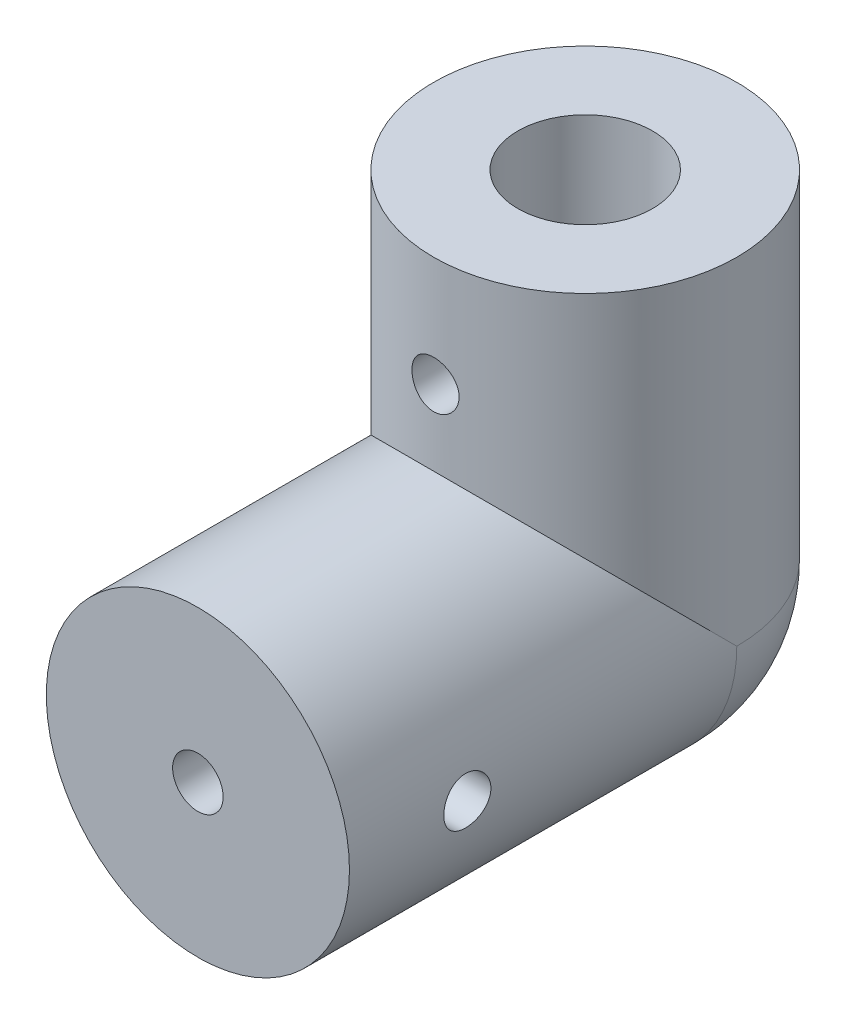
SolidWorks part; units mm, degrees
ref_plane "Alzado" through (0, 0, 0) normal (0, 0, 1) x (1, 0, 0)
ref_plane "Planta" through (0, 0, 0) normal (0, 1, 0) x (1, 0, 0)
ref_plane "Vista lateral" through (0, 0, 0) normal (1, 0, 0) x (0, 0, -1)
sketch "Croquis1" plane through (0, 0, 0) normal (0, 0, 1) x (1, 0, 0)
  circle A0 centre (0, 0) radius 9
  circle A1 centre (0, 0) radius 1.5
  dimension "D1" = 18
  dimension "D2" = 3
extrude "Saliente-Extruir1" add sketch "Croquis1" along normal blind 15 and the other way blind 8
sketch "Croquis2" plane through (0, 0, 0) normal (0, 1, 0) x (1, 0, 0)
  circle A1 centre (0, 8) radius 4
  circle A2 centre (0, 8) radius 9
  dimension "D1" = 18
  dimension "D2" = 8
  dimension "D3" = 8
extrude "Saliente-Extruir4" add sketch "Croquis2" along normal blind 20
sketch "Croquis6" plane through (0, 0, -8) normal (0, 0, -1) x (-1, 0, 0)
  line L0 (0, 0) -> (0, -9)
  line L1 (0, 0) -> (-9, 0)
  arc A0 (-9, 0) -> (9, 0) centre (0, 0) ccw construction
  arc A1 (-9, 0) -> (0, -9) centre (0, 0) ccw
revolve "Revolución4" add sketch "Croquis6" angle 360 about L0
sketch "Croquis7" plane through (0, 20, 0) normal (0, 1, 0) x (1, 0, 0)
  circle A0 centre (0, 8) radius 4
extrude "Cortar-Extruir1" cut sketch "Croquis7" against normal blind 20
sketch "Croquis8" plane through (0, 0, 15) normal (0, 0, 1) x (1, 0, 0)
  circle A0 centre (0, 0) radius 1.5
  dimension "D1" = 3
extrude "Cortar-Extruir2" cut sketch "Croquis8" against normal blind 15
ref_plane "Plano1" through (-9, 0, 0) normal (-1, 0, 0) x (0, 0, 1)
sketch "Croquis9" plane through (-9, 0, 0) normal (-1, 0, 0) x (0, 0, 1)
  line L0 (8, 9) -> (8, -9) construction
  line L1 (15, 9) -> (1, 9) construction
  line L2 (-8, -9) -> (15, -9) construction
  circle A0 centre (8, 0) radius 1.4
  dimension "D1" = 2.8
extrude "Cortar-Extruir3" cut sketch "Croquis9" against normal through all
ref_plane "Plano2" through (0, 0, -17) normal (0, 0, -1) x (-1, 0, 0)
sketch "Croquis10" plane through (0, 0, -17) normal (0, 0, -1) x (-1, 0, 0)
  line L0 (9, 13.459) -> (-9, 13.459) construction
  line L1 (9, 0) -> (9, 20) construction
  line L2 (-9, 20) -> (-9, 0) construction
  circle A0 centre (0, 13.459) radius 1.4
  dimension "D1" = 2.8
extrude "Cortar-Extruir4" cut sketch "Croquis10" against normal through all and the other way through all
